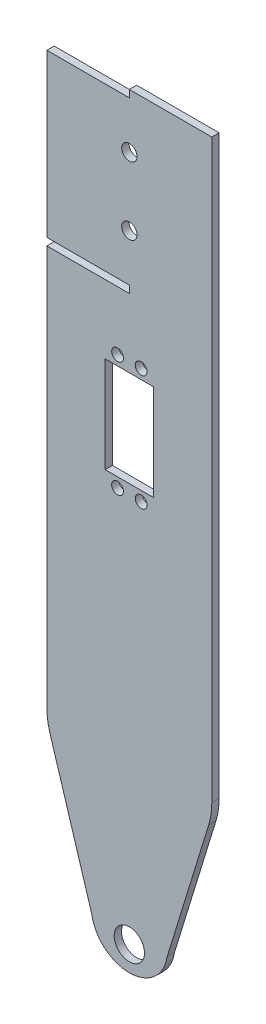
SolidWorks part; units mm, degrees
material "Teak"
ref_plane "Front Plane" through (0, 0, 0) normal (0, 0, 1) x (1, 0, 0)
ref_plane "Top Plane" through (0, 0, 0) normal (0, 1, 0) x (1, 0, 0)
ref_plane "Right Plane" through (0, 0, 0) normal (1, 0, 0) x (0, 0, -1)
sketch "Sketch1" plane through (0, 0, 0) normal (0, 0, 1) x (1, 0, 0)
  line L0 (0, -139.575) -> (0, -174.575) construction
  line L1 (-35, -174.575) -> (35, -174.575)
  line L2 (-35, -174.575) -> (-35, 174.575)
  line L3 (-35, 174.575) -> (35, 174.575)
  line L4 (35, -174.575) -> (35, 174.575)
  line L5 (-35, -174.575) -> (35, 174.575) construction
  line L6 (-35, 174.575) -> (35, -174.575) construction
  line L7 (0, 174.575) -> (0, 0) construction
  line L8 (0, 50.075) -> (-10.25, 50.075) construction
  line L9 (-10.25, 29.725) -> (10.25, 29.725)
  line L10 (-10.25, 29.725) -> (-10.25, 70.425)
  line L11 (-10.25, 70.425) -> (10.25, 70.425)
  line L12 (10.25, 29.725) -> (10.25, 70.425)
  line L13 (-10.25, 29.725) -> (10.25, 70.425) construction
  line L14 (-10.25, 70.425) -> (10.25, 29.725) construction
  circle A0 centre (0, -139.575) radius 6.425
  circle A1 centre (0, 60.425) radius 3.6306 construction
  circle A2 centre (-5, 74.575) radius 2.5
  circle A3 centre (5, 74.575) radius 2.5
  circle A4 centre (5, 25.575) radius 2.5
  circle A5 centre (-5, 25.575) radius 2.5
  point P0 (0, 0)
  point P12 (0, 50.075)
  dimension "D3" = 12.85
  dimension "D12" = 5
  dimension "D1" = 70
  dimension "D2" = 100
  dimension "D4" = 35
  dimension "D5" = 40.7
  dimension "D6" = 20.5
  dimension "D7" = 200
  dimension "D8" = 10
  dimension "D9" = 49
  dimension "D10" = 10
  dimension "D11" = 349.15
extrude "Boss-Extrude1" add sketch "Sketch1" along normal blind 3.1
sketch "Sketch2" plane through (0, 0, 3.1) normal (0, 0, 1) x (1, 0, 0)
  line L0 (0, 0) -> (0, -183.7954) construction
  line L2 (-35, -74.575) -> (-16, -136.2698)
  line L3 (35, -74.575) -> (16, -136.2698)
  line L4 (-35, 174.575) -> (-35, -174.575) construction
  line L5 (-35, -174.575) -> (35, -174.575) construction
  arc A0 (16, -136.2698) -> (-16, -136.2698) centre (0, -133.8728) cw
  dimension "D1" = 32
  dimension "D2" = 100
extrude "Cut-Extrude1" cut sketch "Sketch2" against normal through all and the other way through all
fillet "Fillet2" radius 30 2 edges at (-35, -74.575, 1.55) (35, -74.575, 1.55)
sketch "Sketch4" plane through (0, 0, 3.1) normal (0, 0, 1) x (1, 0, 0)
  line L0 (-35, 174.575) -> (-35, 171.475)
  line L1 (-35, 174.575) -> (0, 174.575)
  line L2 (-35, 171.475) -> (0, 171.475)
  line L3 (0, 174.575) -> (0, 171.475)
  line L5 (-35, 174.575) -> (-35, -70.0601) construction
  line L6 (0, 102.675) -> (-35, 102.675)
  line L7 (0, 102.675) -> (0, 99.575)
  line L8 (-35, 102.675) -> (-35, 99.575)
  line L9 (0, 99.575) -> (-35, 99.575)
  line L10 (0, 0) -> (0, 219.4054) construction
  circle A0 centre (0, 122.675) radius 3.25
  circle A1 centre (0, 151.475) radius 3.25
  dimension "D4" = 6.5
  dimension "D5" = 6.5
  dimension "D1" = 3.1
  dimension "D2" = 3.1
  dimension "D3" = 75
  dimension "D6" = 20
  dimension "D7" = 20
extrude "Cut-Extrude2" cut sketch "Sketch4" against normal through all
equation "\"thick\"= 3.1mm"
equation "\"small_bearing_outer\"=12.9mm"
equation "\"servo1_L\"=40.7mm"
equation "\"servo1_W\"=20.5mm"
equation "\"servo1_H\"=43.5mm"
equation "\"servo1_hL\"=49mm"
equation "\"servo1_hW\"=10mm"
equation "\"servo1_H2\"=27mm"
equation "\"large_bearing_inner\"=2.75in"
equation "\"large_bearing_outer\"=4.75in"
equation "\"large_bearing_thick\"=3/8in"
equation "\"large_bearing_h1\"=3.25in"
equation "\"large_bearing_h2\"=4.25in"
equation "\"D4@Sketch1\"=\"D1@Sketch1\"/2"
equation "\"D5@Sketch1\"=\"servo1_L\""
equation "\"D6@Sketch1\"=\"servo1_W\""
equation "\"D9@Sketch1\"=\"servo1_hL\""
equation "\"D10@Sketch1\"=\"servo1_hW\""
equation "\"D1@Sketch4\"=\"thick\""
equation "\"D2@Sketch4\"=\"thick\""
equation "\"D5@Sketch4\"=\"D4@Sketch4\""
equation "\"D7@Sketch4\"=20"
